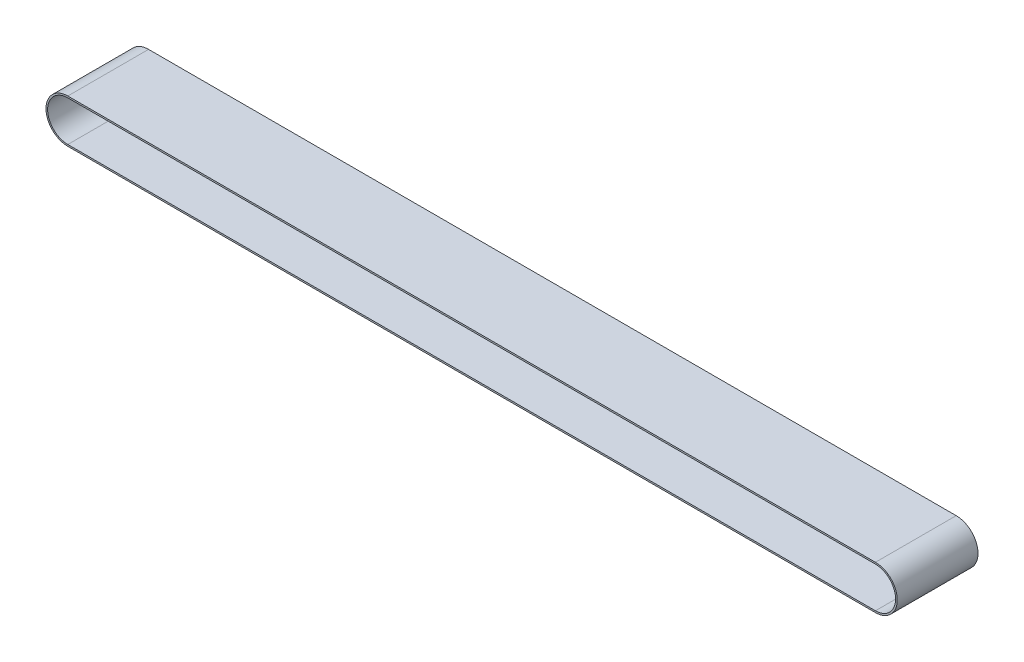
SolidWorks part; units mm, degrees
ref_plane "Piano frontale" through (0, 0, 0) normal (0, 0, 1) x (1, 0, 0)
ref_plane "Piano superiore" through (0, 0, 0) normal (0, 1, 0) x (1, 0, 0)
ref_plane "Piano destro" through (0, 0, 0) normal (1, 0, 0) x (0, 0, -1)
sketch "Schizzo2" plane through (0, 0, 0) normal (0, 0, 1) x (1, 0, 0)
  line L0 (0, 261.6055) -> (0, -211.6055) construction
  line L1 (-500, 25) -> (500, 25)
  line L2 (-500, -25) -> (500, -25)
  arc A0 (-500, 25) -> (-500, -25) centre (-500, 0) ccw
  arc A1 (500, 25) -> (500, -25) centre (500, 0) cw
  point P8 (0, 25)
  point P11 (0, -25)
  dimension "D2" = 50
  dimension "D1" = 500
extrude "Estrusione-Sottile1" add sketch "Schizzo2" along normal blind 100 thin thin type one direction wall 2
